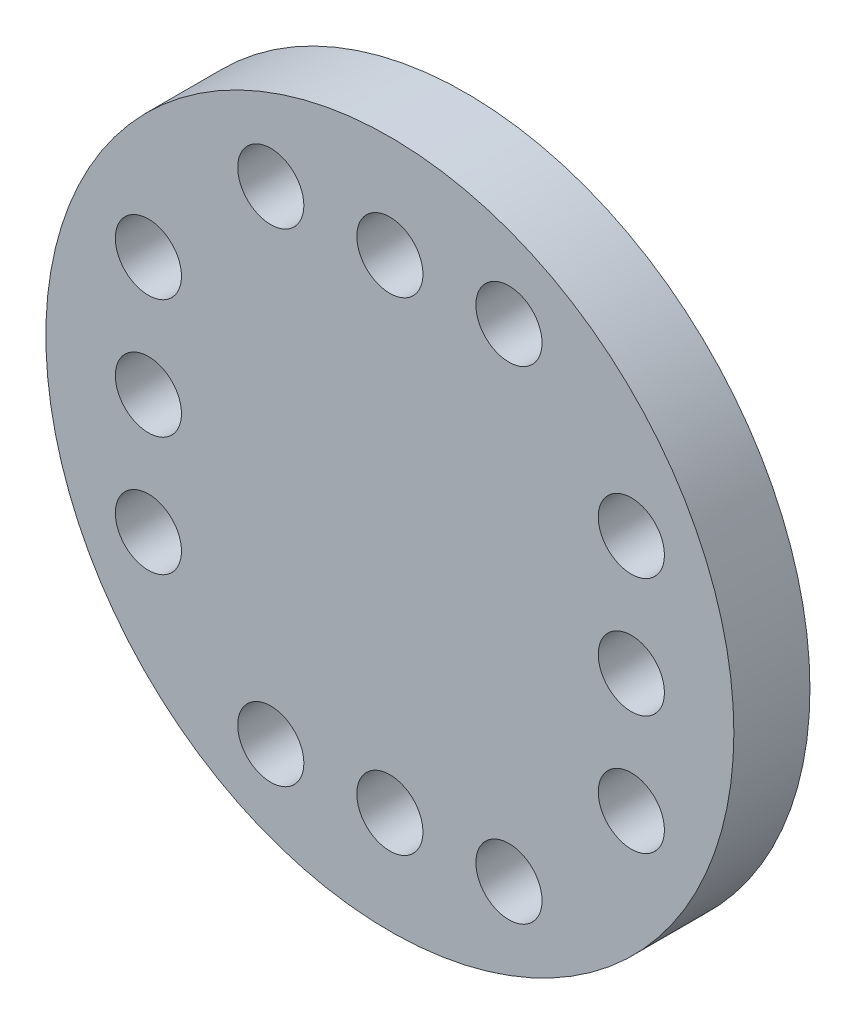
SolidWorks part; units mm, degrees
ref_plane "정면" through (0, 0, 0) normal (0, 0, 1) x (1, 0, 0)
ref_plane "윗면" through (0, 0, 0) normal (0, 1, 0) x (1, 0, 0)
ref_plane "우측면" through (0, 0, 0) normal (1, 0, 0) x (0, 0, -1)
sketch "스케치2" plane through (0, 0, -4) normal (0, 0, 1) x (1, 0, 0)
  circle A0 centre (10.45, 0) radius 4.4
  circle A1 centre (10.45, 0) radius 2.95
  dimension "D1" = 8.8
  dimension "D2" = 5.9
extrude "보스-돌출2" add sketch "스케치2" along normal blind 3 from offset 1
sketch "스케치3" plane through (0, 0, 0) normal (0, 0, 1) x (1, 0, 0)
  circle A0 centre (10.45, 0) radius 10.4
  dimension "D1" = 20.8
extrude "보스-돌출3" add sketch "스케치3" along normal blind 2.3
sketch "스케치5" plane through (0, 0, 2.3) normal (0, 0, 1) x (1, 0, 0)
  line L0 (10.45, 0) -> (10.45, 10.4) construction
  line L1 (10.45, 0) -> (0, 0) construction
  circle A0 centre (10.45, 0) radius 10.4 construction
  circle A1 centre (10.45, 7.3) radius 1
  circle A2 centre (14.05, 7.3) radius 1
  circle A3 centre (6.85, 7.3) radius 1
  circle A4 centre (3.15, 0) radius 1
  circle A5 centre (3.15, 3.6) radius 1
  circle A6 centre (3.15, -3.6) radius 1
  circle A7 centre (10.45, -7.3) radius 1
  circle A8 centre (6.85, -7.3) radius 1
  circle A9 centre (14.05, -7.3) radius 1
  circle A10 centre (17.75, 0) radius 1
  circle A11 centre (17.75, -3.6) radius 1
  circle A12 centre (17.75, 3.6) radius 1
  point P34 (10.45, 0)
  dimension "D1" = 7.3
  dimension "D2" = 2
  dimension "D5" = 4
  dimension "D3" = 2
  dimension "D4" = 2
extrude "컷-돌출1" cut sketch "스케치5" against normal blind 2.3
sketch "스케치6" plane through (0, 0, 2.3) normal (0, 0, 1) x (1, 0, 0)
  line L0 (10.45, -10.4) -> (10.45, 10.4) construction
  line L1 (20.85, 0) -> (0, 0) construction
  circle A0 centre (10.45, 0) radius 10.4 construction
